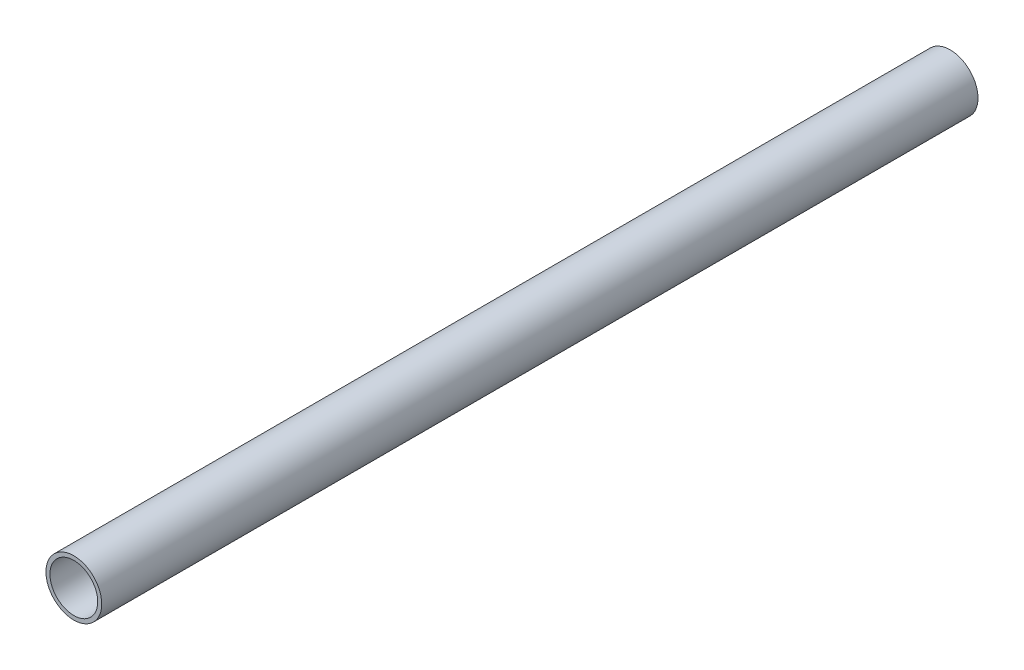
SolidWorks part; units mm, degrees
material "Plástico personalizado"
ref_plane "Plano frontal" through (0, 0, 0) normal (0, 0, 1) x (1, 0, 0)
ref_plane "Plano superior" through (0, 0, 0) normal (0, 1, 0) x (1, 0, 0)
ref_plane "Plano direito" through (0, 0, 0) normal (1, 0, 0) x (0, 0, -1)
sketch "Esboço1" plane through (0, 0, 0) normal (0, 0, 1) x (1, 0, 0)
  circle A0 centre (0, 0) radius 7
  circle A1 centre (0, 0) radius 6
  dimension "D1" = 14
  dimension "D2" = 12
extrude "Ressalto-extrusão1" add sketch "Esboço1" along normal blind 220
